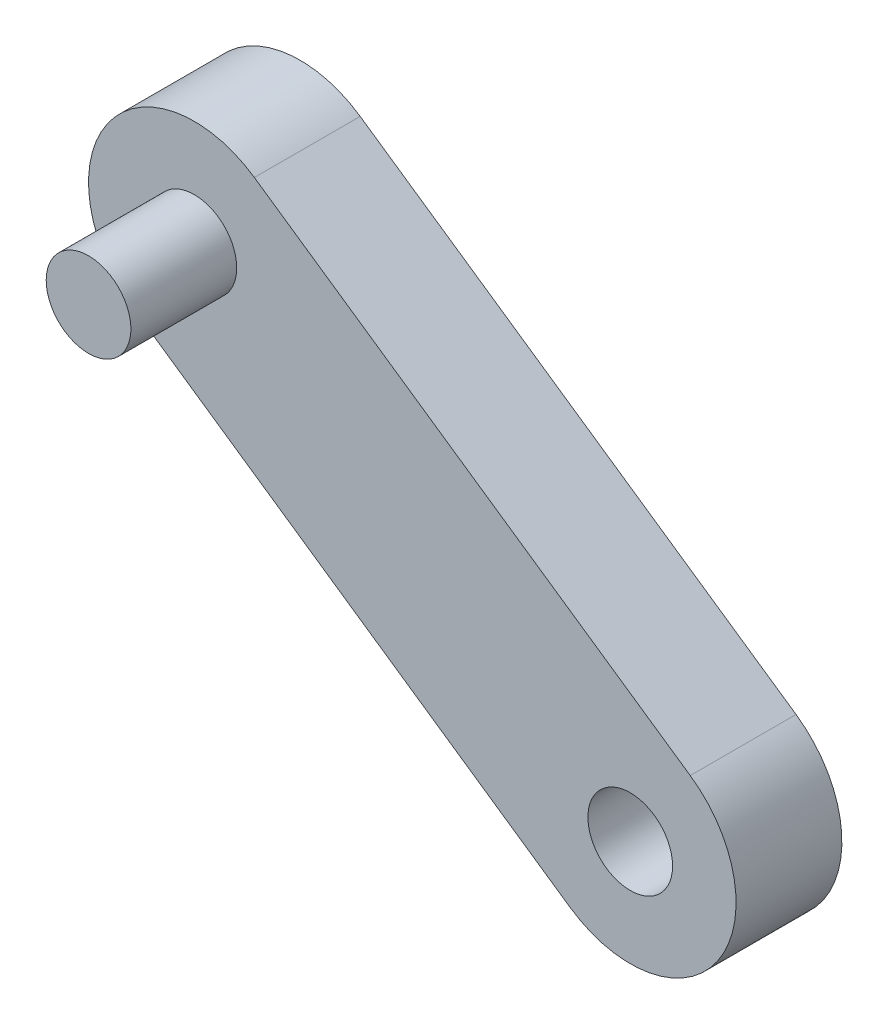
SolidWorks part; units mm, degrees
ref_plane "Front Plane" through (0, 0, 0) normal (0, 0, 1) x (1, 0, 0)
ref_plane "Top Plane" through (0, 0, 0) normal (0, 1, 0) x (1, 0, 0)
ref_plane "Right Plane" through (0, 0, 0) normal (1, 0, 0) x (0, 0, -1)
sketch "Sketch1" plane through (0, 0, 0) normal (0, 0, 1) x (0.9998, -0.022, 0)
  line L0 (0.6447, 52.8572) -> (-25.8837, 70.342) construction
  line L1 (5.01, 49.98) -> (5.01, 69.98) construction
  line L2 (5.01, 69.98) -> (-55.6789, 69.98) construction
  line L3 (-46.2352, 83.6971) -> (-25.3345, 69.98) construction
  line L4 (-46.2352, 83.6971) -> (-43.4918, 87.8772) construction
  line L5 (-43.4918, 87.8772) -> (-48.9786, 79.5169) construction
  line L6 (-43.4918, 87.8772) -> (-22.591, 74.1602)
  line L7 (-48.9786, 79.5169) -> (-28.0779, 65.7999)
  line L8 (-22.591, 74.1602) -> (-28.0779, 65.7999) construction
  circle A0 centre (5.01, 49.98) radius 2 construction
  circle A1 centre (5.01, 49.98) radius 2 construction
  circle A3 centre (-25.3345, 69.98) radius 2
  arc A4 (-29.5092, 72.7316) -> (-29.5146, 72.7234) centre (-25.3345, 69.98) ccw
  circle A5 centre (-46.2352, 83.6971) radius 2 construction
  circle A6 centre (-46.2352, 83.6971) radius 2
  arc A7 (-43.4918, 87.8772) -> (-48.9786, 79.5169) centre (-46.2352, 83.6971) ccw
  arc A8 (-28.0779, 65.7999) -> (-22.591, 74.1602) centre (-25.3345, 69.98) ccw
  point P18 (-25.3345, 69.98)
  dimension "D1" = 5
  dimension "D2" = 5
  dimension "D4" = 4
  dimension "D5" = 4
  dimension "D6" = 10
  dimension "D3" = 20
  dimension "D7" = 25
extrude "Boss-Extrude1" add sketch "Sketch1" along normal blind 5
sketch "Sketch2" plane through (0, 0, 0) normal (0, 0, -1) x (-1, 0, 0)
  circle A0 centre (44.3801, 84.6953) radius 2
extrude "Boss-Extrude2" add sketch "Sketch2" against normal blind 10 separate body
move or copy body "Body-Move/Copy1" [suppressed] bodies to move or copy 101 102
